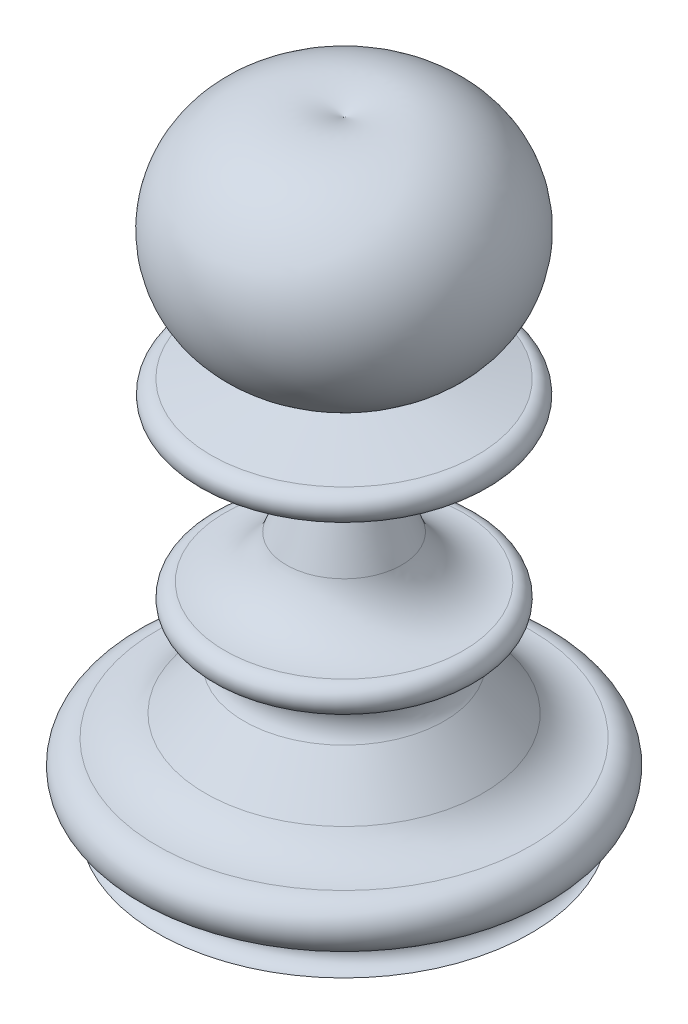
SolidWorks part; units mm, degrees
ref_plane "Front Plane" through (0, 0, 0) normal (0, 0, 1) x (1, 0, 0)
ref_plane "Top Plane" through (0, 0, 0) normal (0, 1, 0) x (1, 0, 0)
ref_plane "Right Plane" through (0, 0, 0) normal (1, 0, 0) x (0, 0, -1)
sketch "Sketch1" plane through (0, 0, 0) normal (0, 0, 1) x (1, 0, 0)
  line L0 (0, 0) -> (-21.0243, 0)
  line L1 (-15.616, 10.9419) -> (-11.2597, 15.7957)
  line L2 (-6.4788, 28.6329) -> (-4.7004, 33.4825)
  line L3 (-4.7004, 33.4825) -> (-4.7004, 40.4917)
  line L4 (-4.7004, 40.4917) -> (-14.9856, 40.4917)
  line L5 (0, 0) -> (0, 81.706) construction
  line L6 (-14.9856, 43.6023) -> (-2.0707, 46.5091)
  line L7 (0, 69.0696) -> (0, 0)
  arc A0 (-21.0243, 0) -> (-21.0243, 3.1735) centre (-21.0243, 1.5867) ccw
  arc A1 (-21.0243, 3.1735) -> (-21.0243, 8.5287) centre (-21.0243, 5.8511) cw
  arc A2 (-21.0243, 8.5287) -> (-15.616, 10.9419) centre (-21.0243, 15.7957) ccw
  arc A3 (-11.2597, 15.7957) -> (-13.4379, 20.6772) centre (-13.4379, 17.7506) ccw
  arc A4 (-13.4379, 20.6772) -> (-13.4379, 23.7727) centre (-13.4379, 22.225) cw
  arc A5 (-13.4379, 23.7727) -> (-6.4788, 28.6329) centre (-13.4379, 31.1849) ccw
  arc A6 (-14.9856, 40.4917) -> (-14.9856, 43.6023) centre (-14.9856, 42.047) cw
  arc A7 (-2.0707, 46.5091) -> (0, 69.0696) centre (-4.685, 58.1243) cw
revolve "Revolve1" add sketch "Sketch1" angle 360 about L5
